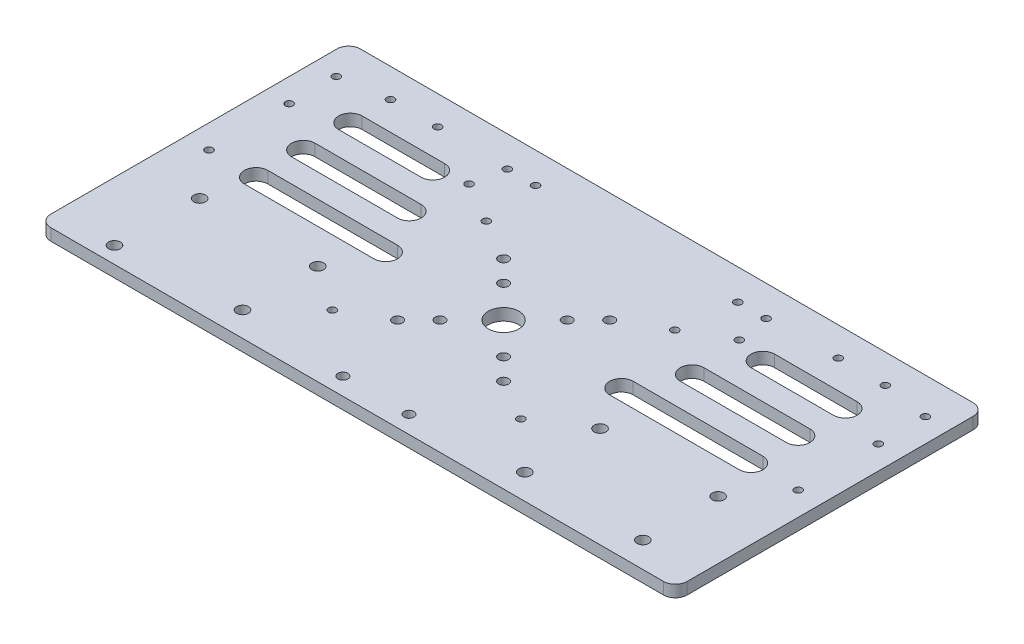
SolidWorks part; units mm, degrees
material "Thornel Mat VMA"
ref_plane "前视基准面" through (0, 0, 0) normal (0, 0, 1) x (1, 0, 0)
ref_plane "上视基准面" through (0, 0, 0) normal (0, 1, 0) x (1, 0, 0)
ref_plane "右视基准面" through (0, 0, 0) normal (1, 0, 0) x (0, 0, -1)
sketch "草图1" plane through (0, 0, 0) normal (0, 1, 0) x (1, 0, 0)
  line L1 (-140, 65) -> (140, 65)
  line L2 (-140, 65) -> (-140, -65)
  line L3 (-140, -65) -> (140, -65)
  line L4 (140, 65) -> (140, -65)
  line L5 (-140, 65) -> (140, -65) construction
  line L6 (-140, -65) -> (140, 65) construction
  circle A0 centre (0, 0) radius 6.5
  dimension "D1" = 13
  dimension "D2" = 280
  dimension "D3" = 130
extrude "凸台-拉伸1" add sketch "草图1" along normal blind 5
sketch "草图2" plane through (0, 5, 0) normal (0, 1, 0) x (1, 0, 0)
  line L0 (0, 65) -> (0, -65) construction
  line L1 (140, 65) -> (-140, 65) construction
  line L2 (-140, -65) -> (140, -65) construction
  line L3 (-125, 65) -> (-125, -65) construction
  line L4 (125, 65) -> (125, -65) construction
  circle A0 centre (-125, 0) radius 1.6
  circle A1 centre (-125, 34) radius 1.6
  circle A2 centre (-125, 54) radius 1.6
  circle A3 centre (-125, -33) radius 1.6
  circle A4 centre (125, 54) radius 1.6
  circle A5 centre (125, 34) radius 1.6
  circle A6 centre (125, 0) radius 1.6
  circle A7 centre (125, -33) radius 1.6
  dimension "D2" = 3.2
  dimension "D3" = 34
  dimension "D4" = 20
  dimension "D5" = 33
  dimension "D1" = 250
extrude "切除-拉伸1" cut sketch "草图2" against normal blind 5
sketch "草图3" plane through (0, 5, 0) normal (0, 1, 0) x (1, 0, 0)
  circle A0 centre (-13.5, 13.5) radius 2.1
  circle A1 centre (-22.5, 22.5) radius 2.1
  circle A2 centre (13.5, 13.5) radius 2.1
  circle A3 centre (22.5, 22.5) radius 2.1
  circle A4 centre (13.5, -13.5) radius 2.1
  circle A5 centre (22.5, -22.5) radius 2.1
  circle A6 centre (-13.5, -13.5) radius 2.1
  circle A7 centre (-22.5, -22.5) radius 2.1
  point P19 (0, 0)
  dimension "D2" = 27
  dimension "D3" = 45
  dimension "D4" = 4.2
  dimension "D1" = 4
extrude "切除-拉伸2" cut sketch "草图3" against normal blind 5
sketch "草图7" plane through (0, 0, 0) normal (0, -1, 0) x (1, 0, 0)
  line L0 (80, -65) -> (23.4918, -32.375)
  line L2 (0, -86.5275) -> (0, 79.2384) construction
  line L3 (80, -65) -> (-80, -65)
  line L5 (170.4768, 0) -> (-167.238, 0) construction
  line L6 (-80, -65) -> (-23.4918, -32.375)
  line L10 (80, 65) -> (-80, 65)
  line L11 (-80, 65) -> (-23.4918, 32.375)
  line L12 (80, 65) -> (23.4918, 32.375)
  line L13 (140, -65) -> (-140, -65) construction
  arc A1 (-23.4918, -32.375) -> (23.4918, -32.375) centre (0, 0) ccw
  arc A2 (-23.4918, 32.375) -> (23.4918, 32.375) centre (0, 0) cw
  dimension "D1" = 40
  dimension "D2" = 160
  dimension "D3" = 120
extrude "切除-拉伸3" cut sketch "草图7" against normal blind 10
sketch "草图8" plane through (0, 0, 0) normal (0, -1, 0) x (1, 0, 0)
  line L0 (140, 0) -> (-140, 0) construction
  line L1 (140, 65) -> (140, -65) construction
  line L2 (-140, -65) -> (-140, 65) construction
  line L3 (0, -52.2182) -> (0, 54.0185) construction
  line L4 (105, 0) -> (50, 0) construction
  line L5 (105, -5) -> (50, -5)
  line L6 (105, 5) -> (50, 5)
  line L7 (105, -20) -> (60, -20) construction
  line L8 (105, -25) -> (60, -25)
  line L9 (105, -15) -> (60, -15)
  line L10 (105, -40) -> (70, -40) construction
  line L11 (105, -45) -> (70, -45)
  line L12 (105, -35) -> (70, -35)
  line L13 (105, 40) -> (70, 40) construction
  line L14 (105, 45) -> (70, 45)
  line L15 (105, 35) -> (70, 35)
  line L16 (105, 20) -> (60, 20) construction
  line L17 (105, 25) -> (60, 25)
  line L18 (105, 15) -> (60, 15)
  line L19 (-105, -40) -> (-70, -40) construction
  line L20 (-105, -45) -> (-70, -45)
  line L21 (-105, -35) -> (-70, -35)
  line L22 (-105, -20) -> (-60, -20) construction
  line L23 (-105, -25) -> (-60, -25)
  line L24 (-105, -15) -> (-60, -15)
  line L25 (-105, 0) -> (-50, 0) construction
  line L26 (-105, -5) -> (-50, -5)
  line L27 (-105, 5) -> (-50, 5)
  line L28 (-105, 20) -> (-60, 20) construction
  line L29 (-105, 25) -> (-60, 25)
  line L30 (-105, 15) -> (-60, 15)
  line L31 (-105, 40) -> (-70, 40) construction
  line L32 (-105, 45) -> (-70, 45)
  line L33 (-105, 35) -> (-70, 35)
  arc A0 (105, -5) -> (105, 5) centre (105, 0) ccw
  arc A1 (50, 5) -> (50, -5) centre (50, 0) ccw
  arc A2 (105, -25) -> (105, -15) centre (105, -20) ccw
  arc A3 (60, -15) -> (60, -25) centre (60, -20) ccw
  arc A4 (105, -45) -> (105, -35) centre (105, -40) ccw
  arc A5 (70, -35) -> (70, -45) centre (70, -40) ccw
  arc A6 (105, 45) -> (105, 35) centre (105, 40) cw
  arc A7 (70, 35) -> (70, 45) centre (70, 40) cw
  arc A8 (105, 25) -> (105, 15) centre (105, 20) cw
  arc A9 (60, 15) -> (60, 25) centre (60, 20) cw
  arc A10 (-105, -45) -> (-105, -35) centre (-105, -40) cw
  arc A11 (-70, -35) -> (-70, -45) centre (-70, -40) cw
  arc A12 (-105, -25) -> (-105, -15) centre (-105, -20) cw
  arc A13 (-60, -15) -> (-60, -25) centre (-60, -20) cw
  arc A14 (-105, -5) -> (-105, 5) centre (-105, 0) cw
  arc A15 (-50, 5) -> (-50, -5) centre (-50, 0) cw
  arc A16 (-105, 25) -> (-105, 15) centre (-105, 20) ccw
  arc A17 (-60, 15) -> (-60, 25) centre (-60, 20) ccw
  arc A18 (-105, 45) -> (-105, 35) centre (-105, 40) ccw
  arc A19 (-70, 35) -> (-70, 45) centre (-70, 40) ccw
  point P11 (77.5, 0)
  point P16 (82.5, -20)
  point P23 (87.5, -40)
  point P36 (87.5, 40)
  point P43 (82.5, 20)
  point P50 (-87.5, -40)
  point P57 (-82.5, -20)
  point P64 (-77.5, 0)
  point P71 (-82.5, 20)
  point P78 (-87.5, 40)
  dimension "D3" = 50
  dimension "D1" = 10
  dimension "D2" = 35
  dimension "D4" = 10
  dimension "D5" = 10
  dimension "D6" = 10
  dimension "D7" = 10
extrude "切除-拉伸4" cut sketch "草图8" against normal blind 10
sketch "草图9" plane through (0, 0, 0) normal (0, -1, 0) x (1, 0, 0)
  line L0 (115, -65) -> (115, 65)
  line L1 (140, -65) -> (80, -65) construction
  line L2 (80, 65) -> (140, 65) construction
  line L3 (-115, -65) -> (-115, 65)
  line L4 (-80, -65) -> (-140, -65) construction
  line L5 (-140, 65) -> (-80, 65) construction
  line L6 (140, 65) -> (140, -65) construction
  line L7 (-140, -65) -> (-140, 65) construction
  dimension "D1" = 25
  dimension "D2" = 25
split line "分割线3"
sketch "草图10" plane through (0, 5, 0) normal (0, 1, 0) x (1, 0, 0)
  circle A0 centre (0, 0) radius 35
  dimension "D1" = 70
split line "分割线4" [suppressed]
sketch "草图11" plane through (0, 0, 0) normal (0, -1, 0) x (1, 0, 0)
  line L0 (140, -57) -> (-140, -57) construction
  line L1 (140, 65) -> (140, -65) construction
  line L2 (-140, -65) -> (-140, 65) construction
  line L3 (0, -85.8273) -> (0, 67.278) construction
  line L4 (-30.3148, -27.0766) -> (-73.0127, -51.7283) construction
  line L5 (-23.4918, -32.375) -> (-80, -65) construction
  line L6 (-80, -65) -> (-115, -65) construction
  line L7 (148.0498, 0) -> (-156.1544, 0) construction
  circle A0 centre (-105, -57) radius 1.6
  circle A1 centre (-85, -57) radius 1.6
  circle A2 centre (-57.3205, -42.6684) radius 1.6
  circle A3 centre (-40, -32.6684) radius 1.6
  circle A4 centre (40, -32.6684) radius 1.6
  circle A5 centre (57.3205, -42.6684) radius 1.6
  circle A6 centre (105, -57) radius 1.6
  circle A7 centre (85, -57) radius 1.6
  circle A8 centre (-105, 57) radius 1.6
  circle A9 centre (-85, 57) radius 1.6
  circle A10 centre (-57.3205, 42.6684) radius 1.6
  circle A11 centre (-40, 32.6684) radius 1.6
  circle A12 centre (40, 32.6684) radius 1.6
  circle A13 centre (57.3205, 42.6684) radius 1.6
  circle A14 centre (85, 57) radius 1.6
  circle A15 centre (105, 57) radius 1.6
  dimension "D3" = 3.2
  dimension "D4" = 35
  dimension "D5" = 20
  dimension "D6" = 20
  dimension "D7" = 80
  dimension "D1" = 8
  dimension "D2" = 8
extrude "切除-拉伸5" cut sketch "草图11" against normal blind 10
fillet "圆角1" radius 20 4 edges at (-23.4918, 2.5, -32.375) (23.4918, 2.5, -32.375) (-23.4918, 2.5, 32.375) (23.4918, 2.5, 32.375)
fillet "圆角3" radius 20 4 edges at (80, 2.5, -65) (80, 2.5, 65) (-80, 2.5, 65) (-80, 2.5, -65)
sketch "草图12" plane through (0, 5, 0) normal (0, 1, 0) x (1, 0, 0)
  line L0 (0, 0) -> (0, -148.9842) construction
  line L2 (140, -5) -> (75, -5)
  line L3 (140, -5) -> (140, -65)
  line L4 (140, -65) -> (75, -65)
  line L5 (75, -5) -> (75, -65)
  line L6 (85.359, -65) -> (140, -65) construction
  line L7 (140, -65) -> (140, 65) construction
  line L8 (50, -5) -> (105, -5) construction
  line L9 (-75, -5) -> (-75, -65)
  line L10 (-140, -65) -> (-75, -65)
  line L11 (-140, -5) -> (-140, -65)
  line L12 (-140, -5) -> (-75, -5)
  dimension "D1" = 65
extrude "切除-拉伸6" cut sketch "草图12" against normal blind 10
sketch "草图13" plane through (0, 5, 0) normal (0, 1, 0) x (1, 0, 0)
  line L0 (-75.359, 62.3205) -> (-33.2328, 37.9989)
  line L1 (33.2328, 37.9989) -> (75.359, 62.3205)
  line L2 (85.359, 65) -> (-85.359, 65)
  arc A0 (-33.2328, 37.9989) -> (-15.4885, 36.8796) centre (-23.2328, 55.3194) ccw
  arc A1 (-15.4885, 36.8796) -> (15.4885, 36.8796) centre (0, 0) cw
  arc A2 (15.4885, 36.8796) -> (33.2328, 37.9989) centre (23.2328, 55.3194) ccw
  arc A3 (75.359, 62.3205) -> (85.359, 65) centre (85.359, 45) cw
  arc A4 (-85.359, 65) -> (-75.359, 62.3205) centre (-85.359, 45) cw
  dimension "D1" = 20
  dimension "D2" = 40
  dimension "D3" = 20
  dimension "D4" = 20
  dimension "D5" = 20
extrude "凸台-拉伸2" add sketch "草图13" against normal up to surface (5 mm away) up to face at (57.3205, 0, -41.0684)
sketch "草图14" plane through (0, 0, 0) normal (0, -1, 0) x (1, 0, 0)
  line L0 (140, -65) -> (140, -69.25)
  line L1 (140, -65) -> (-140, -65)
  line L2 (-140, -65) -> (-140, -69.25)
  line L3 (-140, -69.25) -> (140, -69.25)
extrude "凸台-拉伸3" add sketch "草图14" against normal up to surface (5 mm away) up to face at (0, 5, 17.8595)
sketch "草图15" plane through (0, 0, 0) normal (0, -1, 0) x (1, 0, 0)
  line L0 (140, 5) -> (140, 58.7242)
  line L1 (75, 62.1132) -> (140, 62.1132)
  line L2 (140, 62.1132) -> (140, 58.7242)
  line L3 (140, 5) -> (75, 5)
  line L4 (75, 5) -> (75, 15)
  line L5 (75, 62.1132) -> (33.2328, 37.9989)
  line L6 (-33.2328, 37.9989) -> (-75, 62.1132)
  line L7 (-75, 62.1132) -> (75, 62.1132)
  line L8 (-75, 5) -> (-140, 5)
  line L9 (-50, 5) -> (-75, 5) construction
  line L10 (-140, 5) -> (-140, 62.1132)
  line L12 (-75, 5) -> (-75, 15)
  line L13 (-75, 62.1132) -> (-140, 62.1132)
  line L14 (-75, 15) -> (-60, 15)
  line L15 (-60, 25) -> (-75, 25)
  line L17 (-75, 25) -> (-75, 35)
  line L18 (-75, 35) -> (-70, 35)
  line L19 (-70, 45) -> (-75, 45)
  line L20 (-75, 45) -> (-75, 62.1132)
  line L21 (75, 15) -> (60, 15)
  line L22 (60, 25) -> (75, 25)
  line L23 (75, 25) -> (75, 35)
  line L24 (75, 35) -> (70, 35)
  line L25 (70, 45) -> (75, 45)
  line L26 (75, 45) -> (70, 45) construction
  line L27 (75, 45) -> (75, 62.1132)
  arc A0 (33.2328, 37.9989) -> (15.4885, 36.8796) centre (23.2328, 55.3194) cw
  arc A1 (15.4885, 36.8796) -> (-15.4885, 36.8796) centre (0, 0) ccw
  arc A2 (-15.4885, 36.8796) -> (-33.2328, 37.9989) centre (-23.2328, 55.3194) cw
  arc A3 (-60, 15) -> (-60, 25) centre (-60, 20) ccw
  arc A4 (-70, 35) -> (-70, 45) centre (-70, 40) ccw
  arc A5 (60, 15) -> (60, 25) centre (60, 20) cw
  arc A6 (70, 35) -> (70, 45) centre (70, 40) cw
  dimension "D1" = 20
  dimension "D2" = 40
  dimension "D3" = 20
  dimension "D4" = 5
  dimension "D5" = 5
  dimension "D6" = 5
  dimension "D7" = 5
extrude "凸台-拉伸4" add sketch "草图15" against normal up to surface (5 mm away) contours A6 L24 L23 L22 A5 L21 L4 L3 L0 L2 L1 L27 L25 | A2 A1 A0 L5 L7 L6 | L18 A4 L19 L20 L13 L10 L8 L12 L14 A3 L15 L17 up to face at (0, 5, 17.6234)
sketch "草图16" plane through (0, 5, 0) normal (0, 1, 0) x (1, 0, 0)
  line L0 (-13.5, -13.5) -> (-13.5, -54.6994) construction
  line L1 (13.5, -13.5) -> (14.5529, -54.6994) construction
  circle A1 centre (-13.5, -54.6994) radius 2.1
  circle A2 centre (14.5529, -54.6994) radius 2.1
extrude "切除-拉伸7" cut sketch "草图16" against normal through all
sketch "草图17" plane through (0, 5, 0) normal (0, 1, 0) x (1, 0, 0)
  line L0 (-140, -62.1132) -> (-147.6122, -62.1205)
  line L1 (-140, 69.25) -> (-140, -62.1132)
  line L2 (-147.6122, -62.1205) -> (-147.6122, 69.25)
  line L3 (-147.6122, 69.25) -> (-140, 69.25)
  line L4 (140, 69.25) -> (140, -62.1132)
  line L5 (140, -62.1132) -> (146.3878, -62.1205)
  line L6 (146.3878, -62.1205) -> (146.3878, 69.25)
  line L7 (146.3878, 69.25) -> (140, 69.25)
extrude "凸台-拉伸5" add sketch "草图17" against normal up to surface (5 mm away)
sketch "草图18" plane through (0, 5, 0) normal (0, 1, 0) x (1, 0, 0)
  circle A0 centre (120, -23.1205) radius 2.5
  circle A1 centre (89.3878, -55.2448) radius 2.6243
  circle A2 centre (110.4038, -51.2893) radius 2.5
  circle A3 centre (170, -23.1205) radius 2.5
  circle A4 centre (-59.1736, -19.6855) radius 2.5
  circle A5 centre (-59.0988, -51.6855) radius 2.5
  circle A6 centre (-110, -55.1205) radius 2.5
  circle A7 centre (-109.1735, -19.8024) radius 2.5
extrude "切除-拉伸8" cut sketch "草图18" against normal through all
sketch "草图19" plane through (0, 5, 0) normal (0, 1, 0) x (1, 0, 0)
  line L0 (139.3878, -23.1205) -> (139.3878, -55.1205) construction
  line L1 (120, -23.1205) -> (120, -55.1205) construction
  line L2 (120, -39.1205) -> (139.3878, -39.1205) construction
  line L3 (114.6939, -39.1205) -> (144.6939, -39.1205) construction
  line L4 (114.6939, -34.1205) -> (144.6939, -34.1205)
  line L5 (114.6939, -44.1205) -> (144.6939, -44.1205)
  line L6 (-60, -23.1205) -> (-60, -55.1205) construction
  line L7 (-110, -55.1205) -> (-110, -23.1205) construction
  line L8 (-110, -39.1205) -> (-60, -39.1205) construction
  line L9 (-130.6122, -39.1205) -> (-39.3878, -39.1205) construction
  line L10 (-60, -39.1205) -> (120, -39.1205) construction
  line L11 (-130.6122, -34.1205) -> (-39.3878, -34.1205)
  line L12 (-130.6122, -44.1205) -> (-39.3878, -44.1205)
  line L13 (-20.6122, -39.1205) -> (80.6122, -39.1205) construction
  line L15 (-20.6122, -34.1205) -> (80.6122, -34.1205)
  line L16 (-20.6122, -44.1205) -> (80.6122, -44.1205)
  arc A0 (114.6939, -34.1205) -> (114.6939, -44.1205) centre (114.6939, -39.1205) ccw
  arc A1 (144.6939, -44.1205) -> (144.6939, -34.1205) centre (144.6939, -39.1205) ccw
  arc A2 (-130.6122, -34.1205) -> (-130.6122, -44.1205) centre (-130.6122, -39.1205) ccw
  arc A3 (-39.3878, -44.1205) -> (-39.3878, -34.1205) centre (-39.3878, -39.1205) ccw
  arc A4 (-20.6122, -34.1205) -> (-20.6122, -44.1205) centre (-20.6122, -39.1205) ccw
  arc A5 (80.6122, -44.1205) -> (80.6122, -34.1205) centre (80.6122, -39.1205) ccw
  point P12 (129.6939, -39.1205)
  point P31 (-85, -39.1205)
  point P38 (30, -39.1205)
  dimension "D2" = 5
  dimension "D4" = 5
  dimension "D7" = 5
  dimension "D1" = 10
  dimension "D3" = 30
  dimension "D5" = 10
  dimension "D6" = 10
extrude "切除-拉伸9" cut sketch "草图19" against normal through all
sketch "草图20" plane through (0, 5, 0) normal (0, 1, 0) x (1, 0, 0)
  circle A0 centre (-42.6889, 56.25) radius 1.6
  circle A1 centre (-54.6889, 56.25) radius 1.6
  circle A2 centre (43.1341, 56.25) radius 1.6
  circle A3 centre (55.1341, 56.25) radius 1.6
extrude "切除-拉伸10" cut sketch "草图20" against normal through all
fillet "圆角4" radius 2 4 edges at (146.3878, 2.5, -69.25) (146.3878, 2.5, 62.1205) (-147.6122, 2.5, -69.25) (-147.6122, 2.5, 62.1205)
sketch "草图22" plane through (0, 5, 0) normal (0, 1, 0) x (1, 0, 0)
  line L0 (-130.6122, -34.1205) -> (-33.7736, -34.1205)
  line L1 (-33.7736, -34.1205) -> (-33.7736, -44.4242)
  line L2 (-33.7736, -44.4242) -> (-136.2846, -44.4242)
  line L3 (-136.2846, -44.4242) -> (-136.2846, -34.1205)
  line L4 (-136.2846, -34.1205) -> (-130.6122, -34.1205)
extrude "凸台-拉伸9" add sketch "草图22" against normal blind 5
sketch "草图23" plane through (0, 5, 0) normal (0, 1, 0) x (1, 0, 0)
  circle A0 centre (-40, -32.6684) radius 1.6
extrude "切除-拉伸11" cut sketch "草图23" against normal through all
sketch "草图24" plane through (0, 5, 0) normal (0, 1, 0) x (1, 0, 0)
  line L0 (-20.6122, -34.1205) -> (87.3555, -34.1205)
  line L1 (87.3555, -34.1205) -> (87.3555, -44.8356)
  line L2 (87.3555, -44.8356) -> (-26.4123, -44.8356)
  line L3 (-26.4123, -44.8356) -> (-26.4123, -34.1205)
  line L4 (-26.4123, -34.1205) -> (-20.6122, -34.1205)
extrude "凸台-拉伸10" add sketch "草图24" against normal blind 5
sketch "草图25" plane through (0, 5, 0) normal (0, 1, 0) x (1, 0, 0)
  line L0 (114.6939, -34.1205) -> (146.3878, -34.1205)
  line L1 (146.3878, -34.4162) -> (146.3878, 67.25) construction
  line L2 (146.3878, -34.1205) -> (146.3878, -44.5895)
  line L3 (146.3878, -60.1183) -> (146.3878, -43.8249) construction
  line L4 (146.3878, -44.5895) -> (108.6186, -44.5895)
  line L5 (108.6186, -44.5895) -> (108.6186, -33.647)
  line L6 (108.6186, -33.647) -> (114.6939, -34.1205)
extrude "凸台-拉伸11" add sketch "草图25" against normal blind 5
sketch "草图26" plane through (0, 5, 0) normal (0, 1, 0) x (1, 0, 0)
  circle A0 centre (40, -32.6684) radius 1.6
extrude "切除-拉伸12" cut sketch "草图26" against normal through all
sketch "草图27" plane through (0, 5, 0) normal (0, 1, 0) x (1, 0, 0)
  circle A0 centre (120, -23.1205) radius 2.5
  circle A1 centre (110.4038, -51.2893) radius 2.5
  circle A2 centre (89.3878, -55.2448) radius 2.6243
extrude "凸台-拉伸12" add sketch "草图27" against normal blind 5
sketch "草图28" plane through (0, 5, 0) normal (0, 1, 0) x (1, 0, 0)
  circle A0 centre (110.329, -19.2894) radius 2.5
  circle A1 centre (110.4038, -51.2893) radius 2.5
  circle A2 centre (60.4039, -51.4062) radius 2.5
  circle A3 centre (60.3291, -19.4062) radius 2.5
extrude "切除-拉伸13" cut sketch "草图28" against normal through all
sketch "草图29" plane through (0, 5, 0) normal (0, 1, 0) x (1, 0, 0)
  line L1 (-145.6122, 69.25) -> (144.3878, 69.25) construction
  line L2 (135, 527) -> (135, -3) construction
  line L3 (135, 69.25) -> (135, -62.1132)
  line L4 (-140, -62.1132) -> (140, -62.1132) construction
  line L5 (135, 69.25) -> (146.3878, 69.25)
  line L6 (146.3878, 69.25) -> (146.3878, -62.1132)
  line L7 (146.3878, -62.1132) -> (135, -62.1132)
extrude "切除-拉伸14" cut sketch "草图29" against normal through all
sketch "草图30" plane through (0, 5, 0) normal (0, 1, 0) x (1, 0, 0)
  line L1 (-135, 527) -> (-135, -3) construction
  line L2 (-135, 69.25) -> (-135, -62.1132)
  line L3 (-145.6122, 69.25) -> (135, 69.25) construction
  line L4 (-140, -62.1132) -> (135, -62.1132) construction
  line L5 (-135, -62.1132) -> (-147.6122, -62.1132)
  line L6 (-147.6122, -62.1132) -> (-147.6122, 69.25)
  line L7 (-147.6122, 69.25) -> (-135, 69.25)
extrude "切除-拉伸15" cut sketch "草图30" against normal blind 5
fillet "圆角5" radius 5 4 edges at (135, 2.5, -69.25) (135, 2.5, 62.1132) (-135, 2.5, 62.1132) (-135, 2.5, -69.25)
sketch "草图31" plane through (0, 5, 0) normal (0, 1, 0) x (1, 0, 0)
  line L0 (140, -62.1132) -> (144.3858, -61.8848)
  line L1 (144.3858, -61.8848) -> (145.4994, -62.1132)
  line L2 (145.4994, -62.1132) -> (140, -62.6898)
  line L3 (140, -62.6898) -> (140, -62.1132)
extrude "切除-拉伸16" cut sketch "草图31" against normal blind 5
sketch "草图32" plane through (0, 5, 0) normal (0, 1, 0) x (1, 0, 0)
  line L0 (-145.8067, -61.654) -> (-145.8652, -62.6935)
  line L1 (-145.8652, -62.6935) -> (-139.457, -62.5988)
  line L2 (-139.457, -62.5988) -> (-139.5186, -61.4677)
  line L3 (-139.5186, -61.4677) -> (-145.8067, -61.654)
extrude "切除-拉伸17" cut sketch "草图32" against normal blind 5
